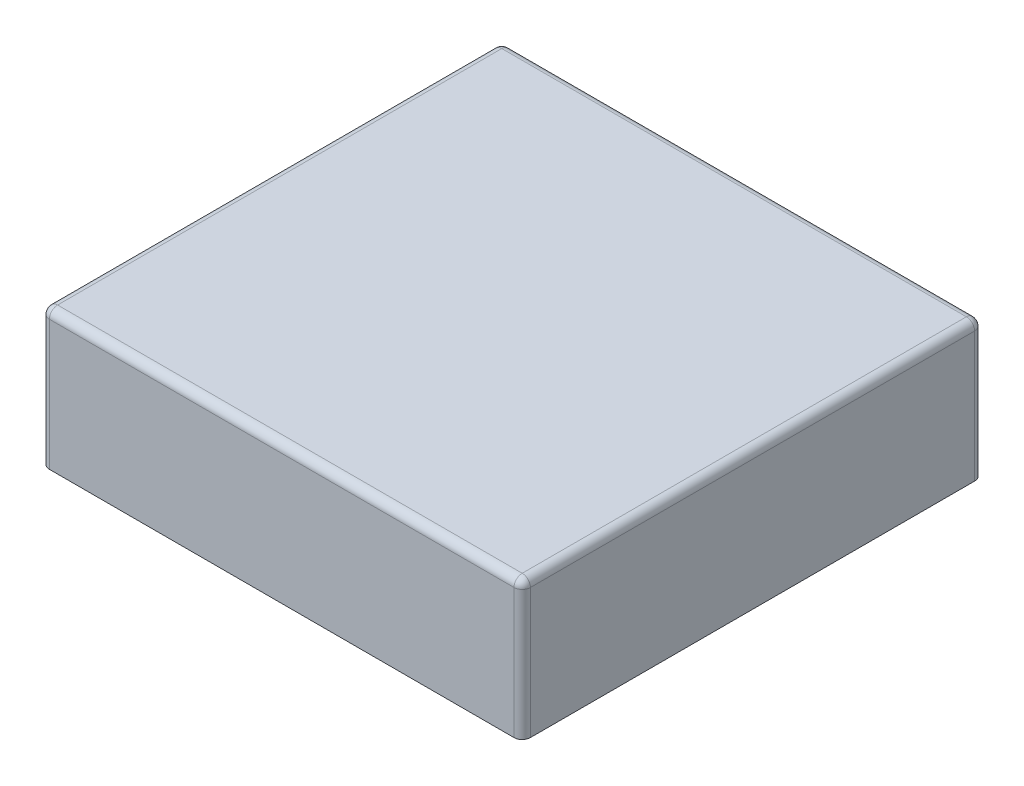
SolidWorks part; units mm, degrees
ref_plane "前视基准面" through (0, 0, 0) normal (0, 0, 1) x (1, 0, 0)
ref_plane "上视基准面" through (0, 0, 0) normal (0, 1, 0) x (1, 0, 0)
ref_plane "右视基准面" through (0, 0, 0) normal (1, 0, 0) x (0, 0, -1)
sketch "草图1" plane through (0, 0, 0) normal (0, 1, 0) x (1, 0, 0)
  line L1 (-58.555, 56.07) -> (58.555, 56.07)
  line L2 (-58.555, 56.07) -> (-58.555, -56.07)
  line L3 (-58.555, -56.07) -> (58.555, -56.07)
  line L4 (58.555, 56.07) -> (58.555, -56.07)
  line L5 (-58.555, 56.07) -> (58.555, -56.07) construction
  line L6 (-58.555, -56.07) -> (58.555, 56.07) construction
  point P0 (0, 0)
  dimension "D1" = 117.11
  dimension "D2" = 112.14
extrude "凸台-拉伸1" add sketch "草图1" along normal blind 33.65
sketch "草图2" plane through (0, 0, 0) normal (0, -1, 0) x (1, 0, 0)
  line L1 (-47, 46) -> (47, 46) construction
  line L2 (-47, 46) -> (-47, -46) construction
  line L3 (-47, -46) -> (47, -46) construction
  line L4 (47, 46) -> (47, -46) construction
  line L5 (-47, 46) -> (47, -46) construction
  line L6 (-47, -46) -> (47, 46) construction
  circle A0 centre (-47, 46) radius 5
  circle A1 centre (47, 46) radius 5
  circle A2 centre (47, -46) radius 5
  circle A3 centre (-47, -46) radius 5
  point P0 (0, 0)
  dimension "D3" = 10
  dimension "D4" = 10
  dimension "D5" = 10
  dimension "D6" = 10
  dimension "D1" = 94
  dimension "D2" = 92
extrude "凸台-拉伸2" add sketch "草图2" along normal blind 3
fillet "圆角1" radius 2 8 edges at (-58.555, 16.825, -56.07) (58.555, 16.825, -56.07) (-58.555, 16.825, 56.07) (58.555, 16.825, 56.07) (0, 33.65, -56.07) (-58.555, 33.65, 0) (58.555, 33.65, 0) (0, 33.65, 56.07)
